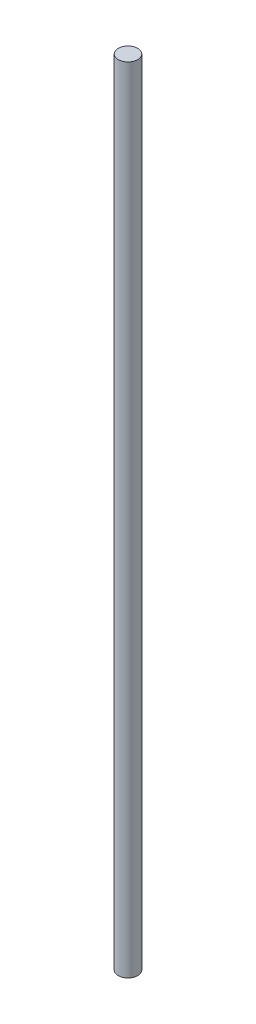
SolidWorks part; units mm, degrees
material "Plain Carbon Steel"
ref_plane "Front Plane" through (0, 0, 0) normal (0, 0, 1) x (1, 0, 0)
ref_plane "Top Plane" through (0, 0, 0) normal (0, 1, 0) x (1, 0, 0)
ref_plane "Right Plane" through (0, 0, 0) normal (1, 0, 0) x (0, 0, -1)
sketch "Sketch1" plane through (0, 0, 0) normal (0, 1, 0) x (1, 0, 0)
  circle A0 centre (0, 0) radius 4.7625
  dimension "D1" = 9.525
extrude "Boss-Extrude1" add sketch "Sketch1" along normal blind 387.35
equation "\"Mid_Coupler_Length\" = 13in"
equation "\"Lead_Screw_Length\" = (\"Mid_Coupler_Length\" + 2*0.375in + 2*.75in)"
equation "\"D1@Boss-Extrude1\"=\"Lead_Screw_Length\""
